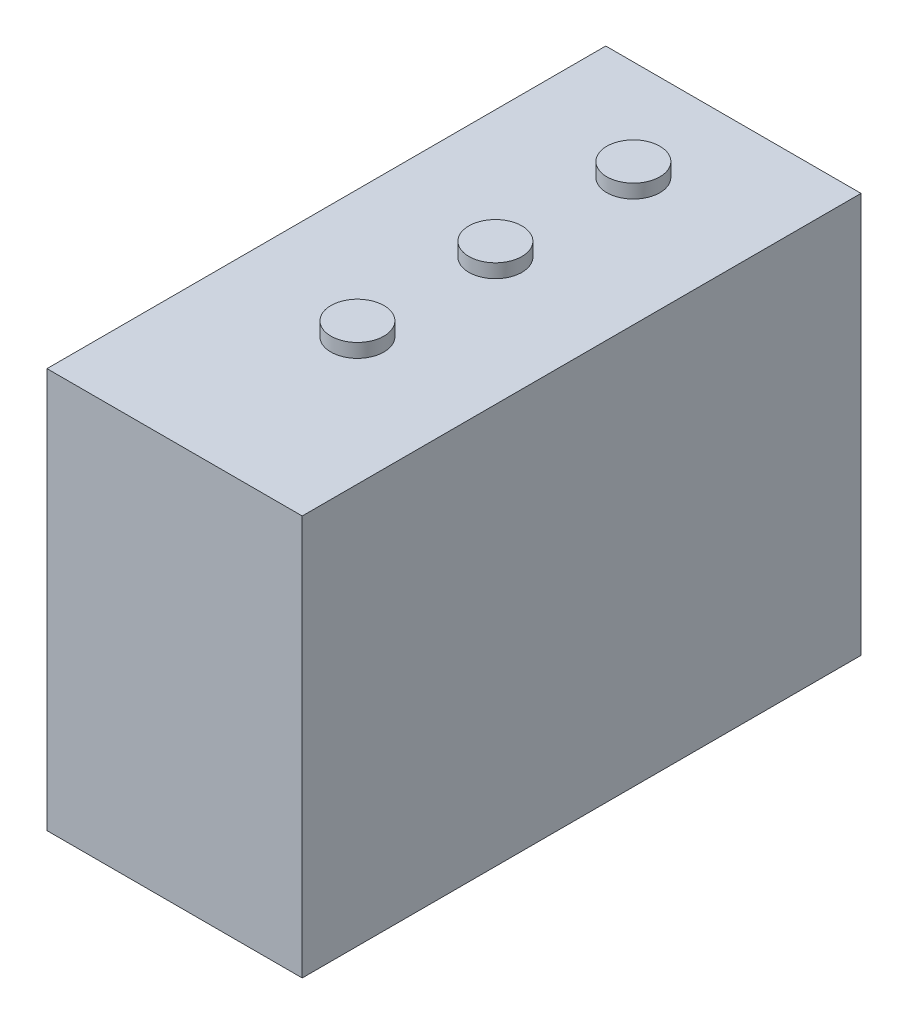
SolidWorks part; units mm, degrees
ref_plane "前视基准面" through (0, 0, 0) normal (0, 0, 1) x (1, 0, 0)
ref_plane "上视基准面" through (0, 0, 0) normal (0, 1, 0) x (1, 0, 0)
ref_plane "右视基准面" through (0, 0, 0) normal (1, 0, 0) x (0, 0, -1)
sketch "草图1" plane through (0, 0, 0) normal (0, 0, 1) x (1, 0, 0)
  line L1 (-18.5, 29) -> (18.5, 29)
  line L2 (-18.5, 29) -> (-18.5, -29)
  line L3 (-18.5, -29) -> (18.5, -29)
  line L4 (18.5, 29) -> (18.5, -29)
  line L5 (-18.5, 29) -> (18.5, -29) construction
  line L6 (-18.5, -29) -> (18.5, 29) construction
  point P0 (0, 0)
  dimension "D1" = 37
  dimension "D2" = 58
extrude "凸台-拉伸1" add sketch "草图1" along normal blind 81
sketch "草图3" plane through (0, 29, 0) normal (0, 1, 0) x (1, 0, 0)
  circle A0 centre (0, -14.5003) radius 3.8427
  circle A1 centre (0, -34.5003) radius 3.8427
  circle A2 centre (0, -54.5003) radius 3.8427
  dimension "D1" = 3
extrude "凸台-拉伸2" add sketch "草图3" along normal blind 2
